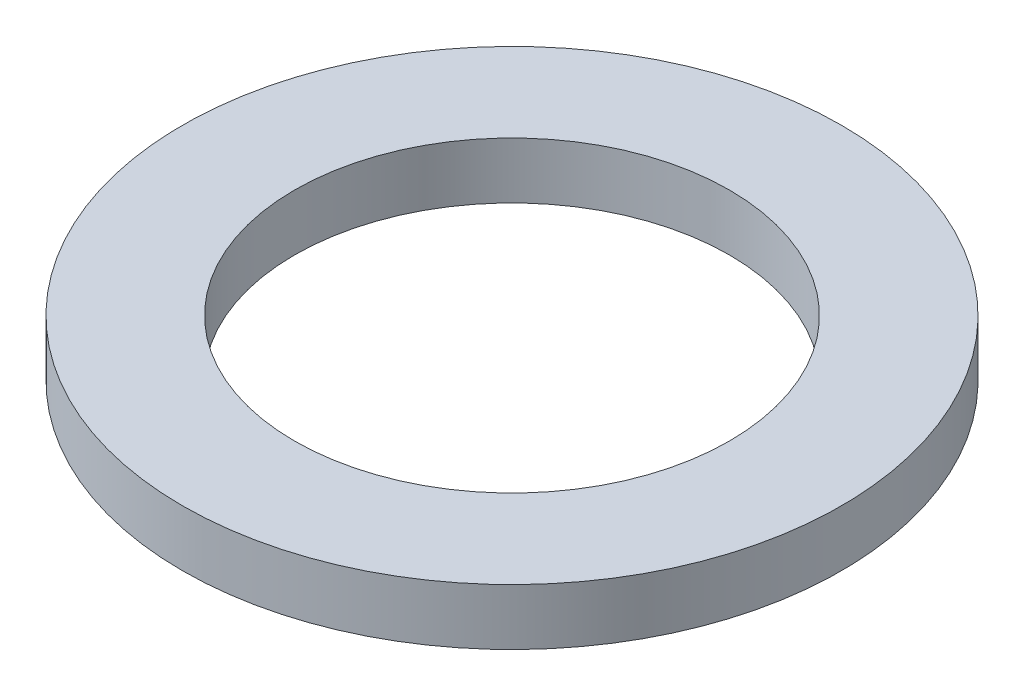
SolidWorks part; units mm, degrees
ref_plane "Front Plane" through (0, 0, 0) normal (0, 0, 1) x (1, 0, 0)
ref_plane "Top Plane" through (0, 0, 0) normal (0, 1, 0) x (1, 0, 0)
ref_plane "Right Plane" through (0, 0, 0) normal (1, 0, 0) x (0, 0, -1)
sketch "Sketch1" plane through (0, 0, 0) normal (0, 1, 0) x (1, 0, 0)
  circle A0 centre (0, 0) radius 4.9085
  circle A1 centre (0, 0) radius 3.2385
  dimension "D1" = 9.8171
  dimension "D2" = 6.477
extrude "Boss-Extrude1" add sketch "Sketch1" along normal blind 0.8382
